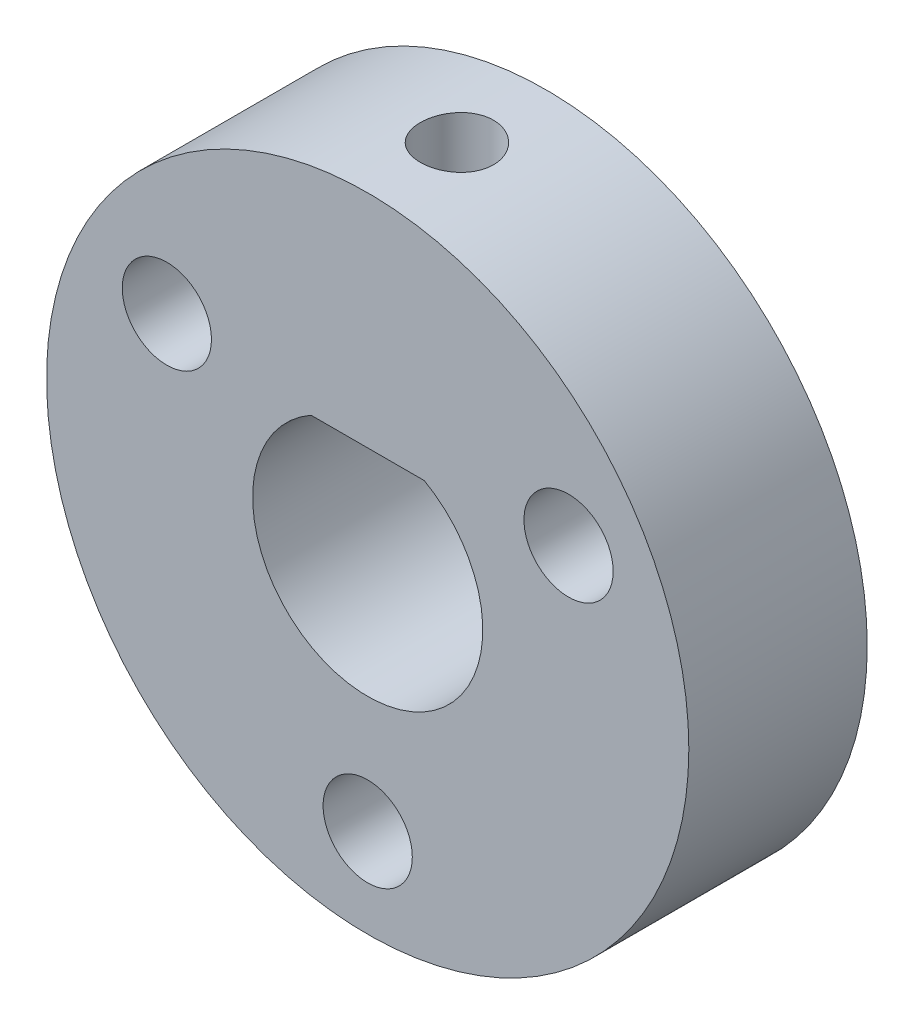
SolidWorks part; units mm, degrees
material "Plain Carbon Steel"
ref_plane "Front Plane" through (0, 0, 0) normal (0, 0, 1) x (1, 0, 0)
ref_plane "Top Plane" through (0, 0, 0) normal (0, 1, 0) x (1, 0, 0)
ref_plane "Right Plane" through (0, 0, 0) normal (1, 0, 0) x (0, 0, -1)
sketch "Sketch1" plane through (0, 0, 0) normal (0, 0, 1) x (1, 0, 0)
  line L0 (-1.5875, 2.8072) -> (1.5875, 2.8072)
  line L1 (-1.5875, 2.7496) -> (1.5875, 2.7496) construction
  line L2 (-3.25, 5.6292) -> (3.25, -5.6292) construction
  line L3 (-5.6292, -3.25) -> (5.6292, 3.25) construction
  line L4 (0, -1000) -> (0, 49000) construction
  circle A0 centre (0, 0) radius 3.225
  circle A1 centre (0, 0) radius 6.5 construction
  circle A2 centre (0, 0) radius 9
  circle A3 centre (0, 0) radius 3.175 construction
  point P12 (0, 0)
  point P16 (0, 0)
  dimension "D1" = 6.45
  dimension "D3" = 13
  dimension "D4" = 18
  dimension "D6" = 6.35
  dimension "D2" = 3.175
  dimension "D5" = 3.175
  dimension "D7" = 30
extrude "Boss-Extrude1" add sketch "Sketch1" along normal mid plane 5 contours A2 A0 | L0 A0
hole_wizard "M2.5 Clearance Hole1" positions "Sketch2" profile "Sketch3" hole size "M2.5" standard "ANSI Metric"
sketch "Sketch2" plane through (0, 0, 2.5) normal (0, 0, 1) x (1, 0, 0)
  point P9 (-3.25, 5.6292)
  point P12 (-5.6292, -3.25)
  point P15 (3.25, -5.6292)
  point P18 (5.6292, 3.25)
sketch "Sketch3" plane through (-3.25, 5.6292, 2.5) normal (1, 0, 0) x (0, -1, 0)
  line L0 (0, 0) -> (0, 5)
  line L1 (0, 5) -> (1.25, 5)
  line L2 (1.25, 5) -> (1.25, 0)
  line L5 (1.25, 0) -> (0, 0)
  line L11 (0, -6.35) -> (0, 107.95) construction
  dimension "Thru Hole Dia." = 2.5
  dimension "Thru Hole Depth" = 5
hole_wizard "M2.5 Clearance Hole2" positions "Sketch4" profile "Sketch5" hole size "M2.5" standard "ANSI Metric" end condition through all
sketch "Sketch4" plane through (0, 0, 2.5) normal (0, 0, 1) x (1, 0, 0)
  line L0 (0, -201000) -> (0, 249000) construction
  circle A0 centre (0, 0) radius 6.5 construction
  point P0 (0, -6.5)
sketch "Sketch5" plane through (0, -6.5, 2.5) normal (1, 0, 0) x (0, -1, 0)
  line L0 (0, 0) -> (0, 5)
  line L1 (0, 5) -> (1.25, 5)
  line L2 (1.25, 5) -> (1.25, 0)
  line L5 (1.25, 0) -> (0, 0)
  line L11 (0, -6.35) -> (0, 107.95) construction
  dimension "Thru Hole Dia." = 2.5
  dimension "Thru Hole Depth" = 5
pattern_circular "CirPattern1" count 3 over 360 about axis through (0, 0, 0) along (0, 0, 1) of "M2.5 Clearance Hole2"
hole_wizard "M2.5x0.45 Tapped Hole1" positions "Sketch6" profile "Sketch7" tap size "M2.5x0.45" standard "ANSI Metric"
sketch "Sketch6" plane through (0, 2.8072, 0) normal (0, -1, 0) x (-1, 0, 0)
  point P0 (0, 0)
sketch "Sketch7" plane through (0, 2.8072, 0) normal (1, 0, 0) x (0, 0, -1)
  line L0 (0, 0) -> (0, 6.1928)
  line L1 (0, 6.1928) -> (1.025, 6.1928)
  line L2 (1.025, 6.1928) -> (1.025, 0)
  line L5 (1.025, 0) -> (0, 0)
  line L11 (0, -6.35) -> (0, 107.95) construction
  dimension "Thru Tap Drill Dia." = 2.05
  dimension "Thru Tap Drill Depth" = 6.1928
cosmetic thread "Hole Thread1" parameters "D2"=2.5
